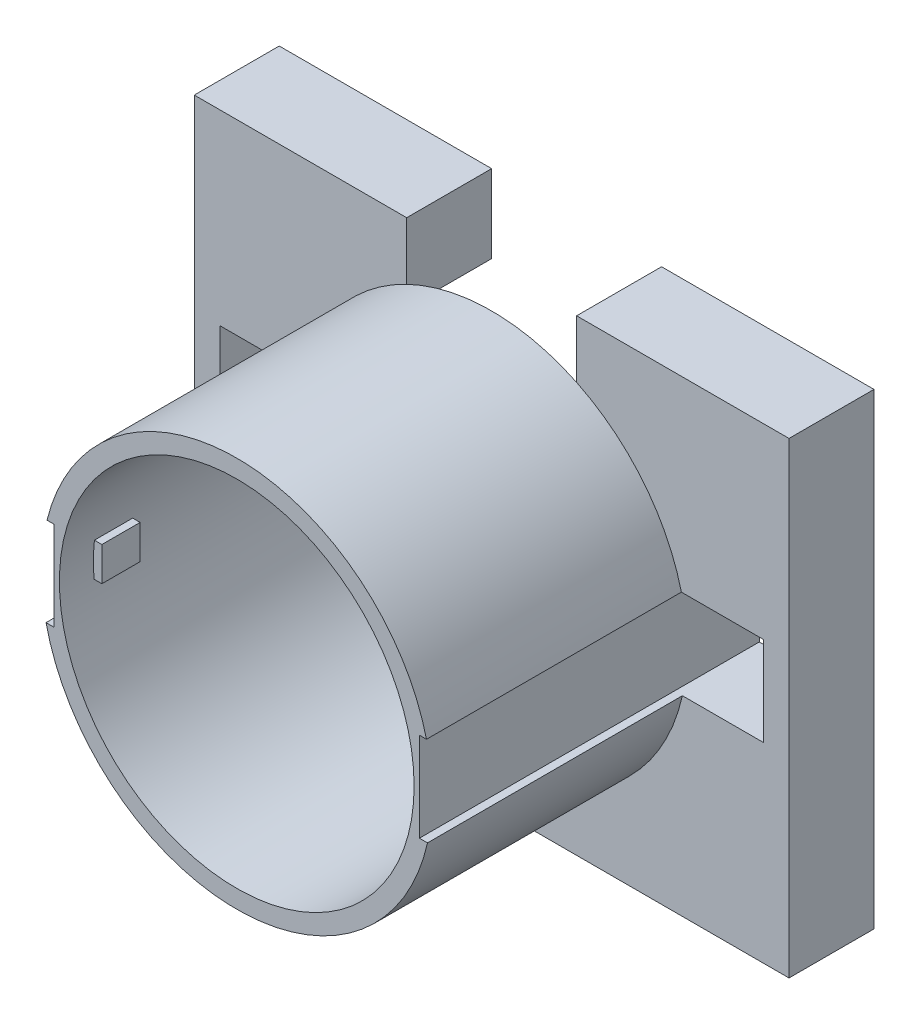
SolidWorks part; units mm, degrees
ref_plane "前基準面" through (0, 0, 0) normal (0, 0, 1) x (1, 0, 0)
ref_plane "上基準面" through (0, 0, 0) normal (0, 1, 0) x (1, 0, 0)
ref_plane "右基準面" through (0, 0, 0) normal (1, 0, 0) x (0, 0, -1)
sketch "草圖1" plane through (0, 0, 0) normal (0, 0, 1) x (1, 0, 0)
  line L1 (-70, 55) -> (70, 55)
  line L2 (-70, 55) -> (-70, -55)
  line L3 (-70, -55) -> (70, -55)
  line L4 (70, 55) -> (70, -55)
  circle A0 centre (0, 0) radius 41.75
  dimension "D1" = 83.5
  dimension "D2" = 70
  dimension "D4" = 55
  dimension "D3" = 110
  dimension "128" = 140
extrude "填料-伸長2" add sketch "草圖1" along normal blind 20
sketch "草圖3" plane through (0, 0, 20) normal (0, 0, 1) x (1, 0, 0)
  circle A0 centre (0, 0) radius 46
  circle A1 centre (0, 0) radius 41.75
  dimension "D1" = 92
  dimension "D2" = 83.5
extrude "填料-伸長3" add sketch "草圖3" along normal blind 60
sketch "草圖4" plane through (0, 0, 0) normal (0, 0, -1) x (-1, 0, 0)
  line L0 (70, 55) -> (70, -55) construction
  line L1 (64, -10) -> (43, -10)
  line L2 (64, -10) -> (64, 11)
  line L3 (64, 11) -> (43, 11)
  line L4 (43, -10) -> (43, 11)
  line L5 (-64, -10) -> (-43, -10)
  line L6 (-64, -10) -> (-64, 11)
  line L7 (-64, 11) -> (-43, 11)
  line L8 (-43, -10) -> (-43, 11)
  line L9 (70, -55) -> (-70, -55) construction
  line L10 (-70, 55) -> (-70, -55) construction
  dimension "D1" = 21
  dimension "D2" = 21
  dimension "D3" = 6
  dimension "D4" = 45
  dimension "D5" = 21
  dimension "D6" = 45
  dimension "D7" = 21
  dimension "D8" = 6
extrude "除料-伸長1" cut sketch "草圖4" against normal through all
ref_plane "平面1" through (-41.75, 0, 0) normal (1, 0, 0) x (0, 0, -1)
sketch "草圖6" plane through (-41.75, 0, 0) normal (1, 0, 0) x (0, 0, -1)
  line L1 (-72, -3.5) -> (-63, -3.5)
  line L2 (-72, -3.5) -> (-72, 4.5)
  line L3 (-72, 4.5) -> (-63, 4.5)
  line L4 (-63, -3.5) -> (-63, 4.5)
  line L5 (-80, 41.75) -> (-80, -41.75) construction
  dimension "D1" = 8
  dimension "D2" = 9
  dimension "D3" = 6.5
  dimension "D4" = 8
extrude "填料-伸長4" add sketch "草圖6" along normal blind 2
ref_plane "平面2" through (41.75, 0, 0) normal (-1, 0, 0) x (0, 0, 1)
sketch "草圖7" plane through (41.75, 0, 0) normal (-1, 0, 0) x (0, 0, 1)
  line L0 (80, -41.75) -> (80, 41.75) construction
  line L1 (72, -3.5) -> (63, -3.5)
  line L2 (72, -3.5) -> (72, 4.5)
  line L3 (72, 4.5) -> (63, 4.5)
  line L4 (63, -3.5) -> (63, 4.5)
  dimension "D1" = 6.5
  dimension "D2" = 8
  dimension "D3" = 9
  dimension "D4" = 8
extrude "填料-伸長5" add sketch "草圖7" along normal blind 2
sketch "草圖8" plane through (0, 55, 0) normal (0, 1, 0) x (1, 0, 0)
  line L0 (-70, -20) -> (70, -20) construction
  line L1 (20, -20) -> (-20, -20)
  line L2 (20, -20) -> (20, 0)
  line L3 (20, 0) -> (-20, 0)
  line L4 (-20, -20) -> (-20, 0)
  line L5 (-70, 0) -> (70, 0) construction
  line L6 (-70, -20) -> (-70, 0) construction
  dimension "D1" = 50
  dimension "D2" = 40
extrude "除料-伸長2" cut sketch "草圖8" against normal up to next
